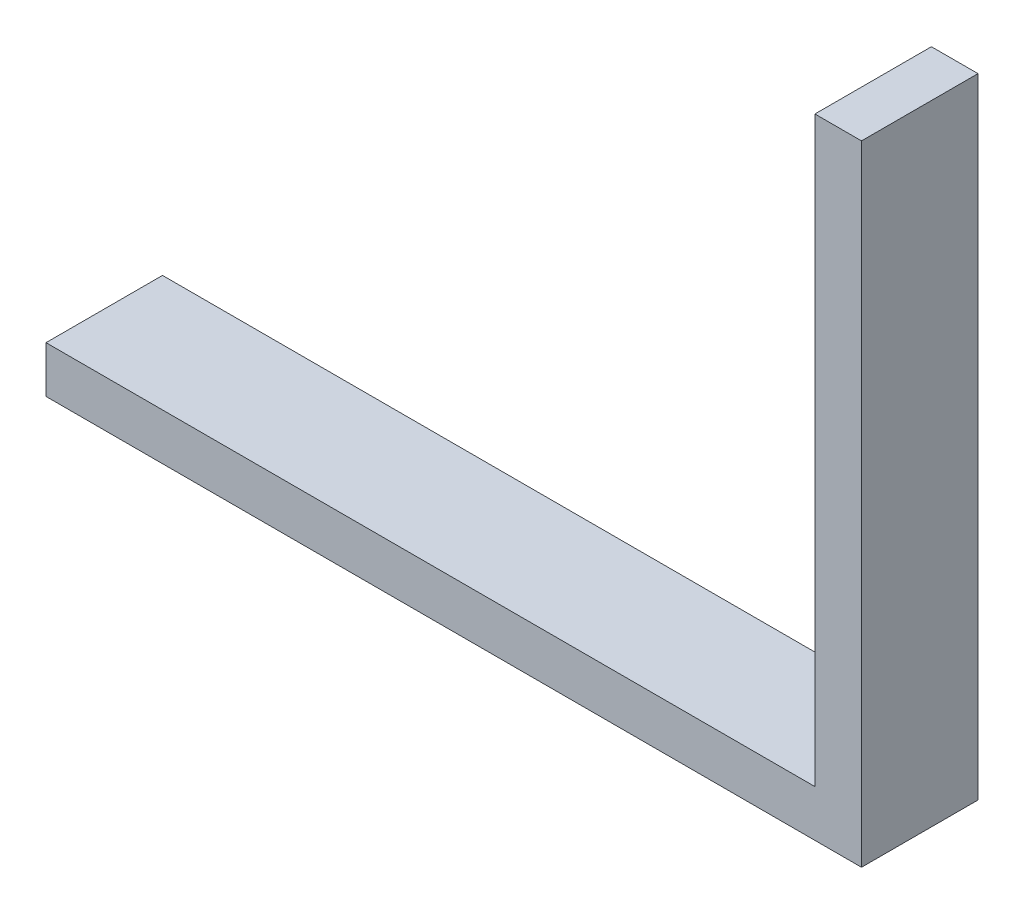
SolidWorks part; units mm, degrees
ref_plane "Front Plane" through (0, 0, 0) normal (0, 0, 1) x (1, 0, 0)
ref_plane "Top Plane" through (0, 0, 0) normal (0, 1, 0) x (1, 0, 0)
ref_plane "Right Plane" through (0, 0, 0) normal (1, 0, 0) x (0, 0, -1)
sketch "Sketch1" plane through (0, 0, 0) normal (0, 1, 0) x (1, 0, 0)
  line L1 (-17.5, 2.5) -> (17.5, 2.5)
  line L2 (-17.5, 2.5) -> (-17.5, -2.5)
  line L3 (-17.5, -2.5) -> (17.5, -2.5)
  line L4 (17.5, 2.5) -> (17.5, -2.5)
  line L5 (-17.5, 2.5) -> (17.5, -2.5) construction
  line L6 (-17.5, -2.5) -> (17.5, 2.5) construction
  point P0 (0, 0)
  dimension "D1" = 5
  dimension "D2" = 35
extrude "Boss-Extrude3" add sketch "Sketch1" along normal blind 2
sketch "Sketch3" plane through (0, 2, 0) normal (0, 1, 0) x (1, 0, 0)
  line L0 (-17.5, -2.5) -> (17.5, -2.5) construction
  line L1 (17.5, 2.5) -> (15.5, 2.5)
  line L2 (17.5, 2.5) -> (17.5, -2.5)
  line L3 (17.5, -2.5) -> (15.5, -2.5)
  line L4 (15.5, 2.5) -> (15.5, -2.5)
  dimension "D1" = 2
extrude "Boss-Extrude4" add sketch "Sketch3" along normal blind 25
